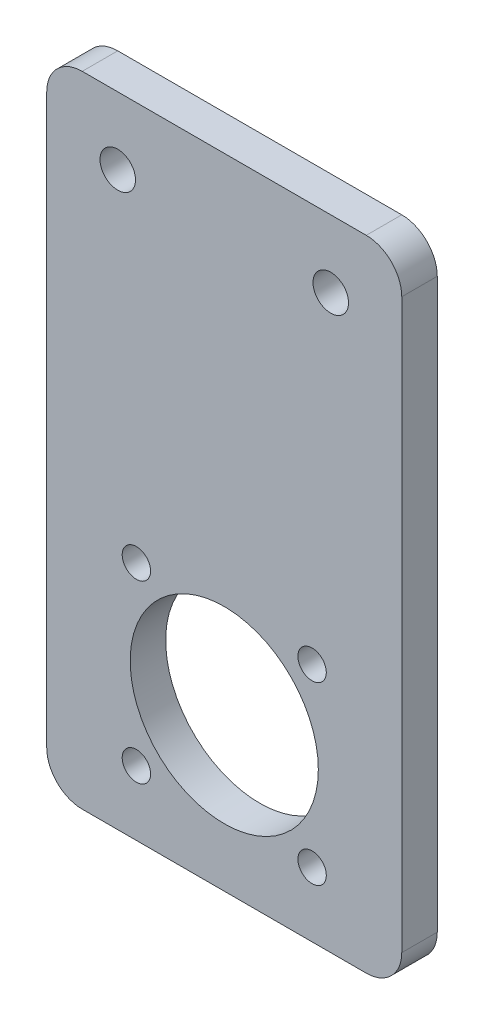
SolidWorks part; units mm, degrees
material "6061 Alloy"
ref_plane "Front Plane" through (0, 0, 0) normal (0, 0, 1) x (1, 0, 0)
ref_plane "Top Plane" through (0, 0, 0) normal (0, 1, 0) x (1, 0, 0)
ref_plane "Right Plane" through (0, 0, 0) normal (1, 0, 0) x (0, 0, -1)
sketch "Sketch1" plane through (0, 0, 0) normal (0, 0, 1) x (1, 0, 0)
  line L0 (25, -68.525) -> (37.3744, -56.1506) construction
  line L1 (0, 0) -> (50, 0)
  line L2 (0, 0) -> (0, -90)
  line L3 (0, -90) -> (50, -90)
  line L4 (50, 0) -> (50, -90)
  line L5 (25, -68.525) -> (38.25, -68.525) construction
  circle A0 centre (10, -9.5) radius 2.5
  circle A1 centre (40, -9.5) radius 2.5
  circle A2 centre (25, -68.525) radius 17.5 construction
  circle A3 centre (37.3744, -56.1506) radius 2
  circle A4 centre (37.3744, -80.8994) radius 2
  circle A5 centre (12.6256, -80.8994) radius 2
  circle A6 centre (12.6256, -56.1506) radius 2
  circle A7 centre (25, -68.525) radius 13.25
  point P22 (25, -68.525)
  dimension "D1" = 5
  dimension "D4" = 30
  dimension "D5" = 10
  dimension "D6" = 35
  dimension "D7" = 25
  dimension "D9" = 4
  dimension "D12" = 26.5
  dimension "D2" = 9.5
  dimension "D3" = 10
  dimension "D8" = 68.525
  dimension "D11" = 90
  dimension "D13" = 45
  dimension "D10" = 4
extrude "Boss-Extrude1" add sketch "Sketch1" along normal blind 5
fillet "Fillet1" radius 5 4 edges at (50, -90, 2.5) (0, -90, 2.5) (0, 0, 2.5) (50, 0, 2.5)
